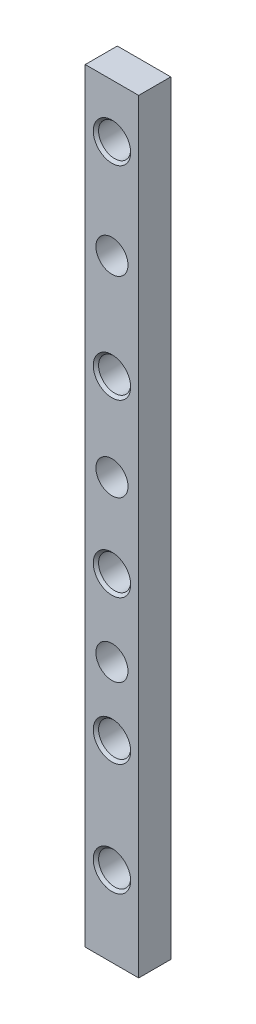
SolidWorks part; units mm, degrees
ref_plane "Front Plane" through (0, 0, 0) normal (0, 0, 1) x (1, 0, 0)
ref_plane "Top Plane" through (0, 0, 0) normal (0, 1, 0) x (1, 0, 0)
ref_plane "Right Plane" through (0, 0, 0) normal (1, 0, 0) x (0, 0, -1)
sketch "Sketch1" plane through (0, 0, 0) normal (0, 0, 1) x (1, 0, 0)
  line L0 (0, 71.5) -> (0, -71.5) construction
  line L1 (-5, -71.5) -> (5, -71.5)
  line L2 (-5, -71.5) -> (-5, 71.5)
  line L3 (-5, 71.5) -> (5, 71.5)
  line L4 (5, -71.5) -> (5, 71.5)
  line L5 (-5, -71.5) -> (5, 71.5) construction
  line L6 (-5, 71.5) -> (5, -71.5) construction
  circle A0 centre (0, -56.5) radius 3
  circle A1 centre (0, -35.5) radius 3
  circle A2 centre (0, -8.5) radius 3
  circle A3 centre (0, 23.5) radius 3
  circle A4 centre (0, 61.5) radius 3
  circle A5 centre (0, 43.0048) radius 3
  circle A6 centre (0, 7.1377) radius 3
  circle A7 centre (0, -22.7933) radius 3
  point P0 (0, 0)
  dimension "D1" = 6
  dimension "D4" = 6
  dimension "D6" = 6
  dimension "D8" = 6
  dimension "D10" = 6
  dimension "D13" = 6
  dimension "D14" = 6
  dimension "D15" = 6
  dimension "D2" = 10
  dimension "D3" = 15
  dimension "D5" = 21
  dimension "D7" = 27
  dimension "D9" = 32
  dimension "D11" = 10
  dimension "D12" = 38
extrude "Boss-Extrude1" add sketch "Sketch1" along normal blind 6
chamfer "Chamfer1" distance 0.5 angle 45 5 edges at (3, 61.5, 6) (3, 23.5, 6) (3, -8.5, 6) (3, -35.5, 6) (3, -56.5, 6)
